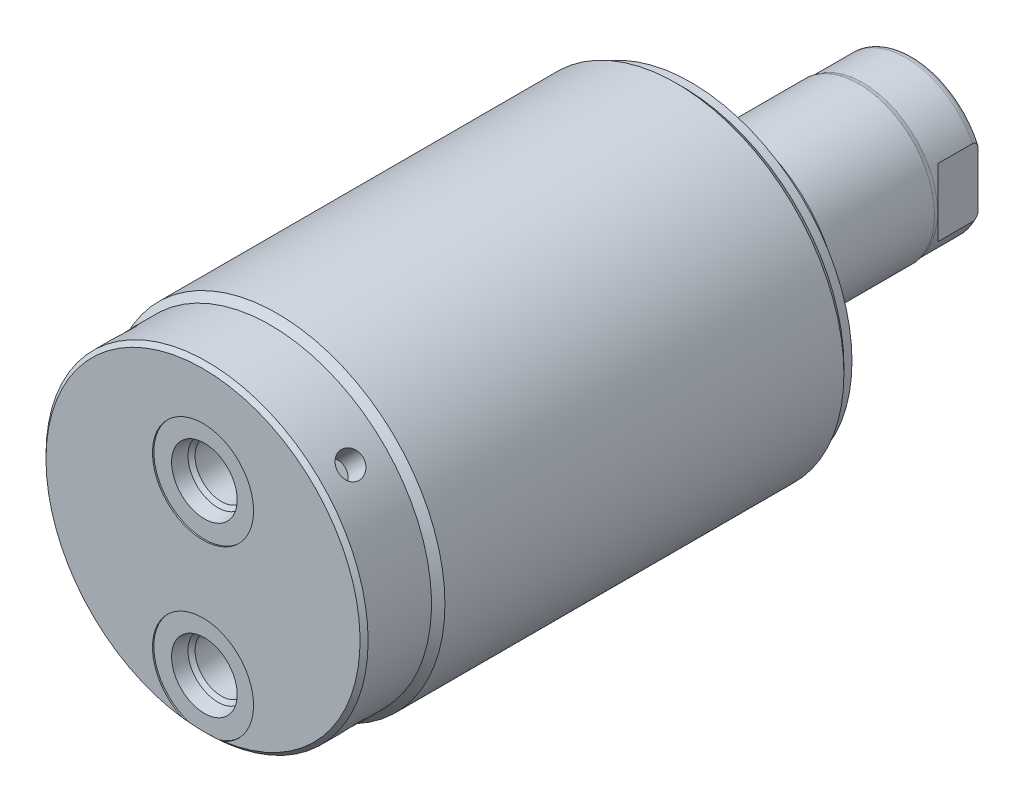
SolidWorks part; units mm, degrees
material "Alloy Steel"
ref_plane "Front Plane" through (0, 0, 0) normal (0, 0, 1) x (1, 0, 0)
ref_plane "Top Plane" through (0, 0, 0) normal (0, 1, 0) x (1, 0, 0)
ref_plane "Right Plane" through (0, 0, 0) normal (1, 0, 0) x (0, 0, -1)
ref_plane "Plane1" through (0, 0, 0) normal (0, 0, 1) x (1, 0, 0)
sketch "Sketch1" plane through (0, 0, 0) normal (0, 0, 1) x (1, 0, 0)
  circle A0 centre (0, 0) radius 31.623
  dimension "D1" = 63.246
extrude "Extrude1" add sketch "Sketch1" along normal blind 91.948
sketch "Sketch2" plane through (0, 0, 0) normal (0, 1, 0) x (1, 0, 0)
  line L0 (31.623, -91.948) -> (31.623, -77.978)
  line L1 (31.623, -77.978) -> (30.353, -79.248)
  line L2 (30.353, -79.248) -> (30.353, -91.948)
  line L3 (30.353, -91.948) -> (31.623, -91.948)
  line L4 (0, 0) -> (0, -24.4965) construction
  line L5 (-31.623, -91.948) -> (31.623, -91.948) construction
  line L6 (31.623, -91.948) -> (31.623, 0) construction
  dimension "D1" = 12.7
  dimension "D2" = 60.706
  dimension "D3" = 45
revolve "Cut-Revolve1" cut sketch "Sketch2" angle 360 about L4
sketch "Sketch3" plane through (0, 0, 0) normal (0, 1, 0) x (1, 0, 0)
  line L0 (30.353, 0) -> (30.353, -1.524)
  line L1 (30.353, -1.524) -> (31.623, -2.794)
  line L2 (31.623, -2.794) -> (31.623, 0)
  line L3 (31.623, 0) -> (30.353, 0)
  line L4 (0, 0) -> (0, 3.0455) construction
  line L6 (31.623, 0) -> (-31.623, 0) construction
  line L7 (31.623, -77.978) -> (31.623, 0) construction
  dimension "D1" = 45
  dimension "D2" = 1.524
  dimension "D3" = 60.706
revolve "Cut-Revolve2" cut sketch "Sketch3" angle 360 about L4
sketch "S2D0002" plane through (0, 0, 0) normal (1, 0, 0) x (0, -1, 0)
  line L0 (-4.9403, -91.694) -> (-1.6002, -91.694)
  line L1 (-4.9403, -91.694) -> (-5.4829, -89.1413)
  line L2 (-5.4829, -89.1413) -> (-6.1468, -88.4774)
  line L3 (-6.1468, -88.4774) -> (-6.1468, -77.724)
  line L4 (-6.1468, -77.724) -> (-11.1252, -77.724)
  line L5 (-11.1252, -77.724) -> (-11.1252, -91.948)
  line L6 (-11.1252, -14.6685) -> (-11.1252, 0.6985) construction
  line L8 (-1.6002, -91.694) -> (-1.6002, -91.948)
  line L9 (-30.353, -91.948) -> (30.353, -91.948) construction
  line L10 (-1.6002, -91.948) -> (-11.1252, -91.948)
  dimension "D1" = 19.05
  dimension "D2" = 9.9568
  dimension "D3" = 0.254
  dimension "D4" = 12.3698
  dimension "D5" = 12
  dimension "D6" = 45
  dimension "D7" = 2.5527
  dimension "D8" = 13.97
  dimension "D9" = 11.1252
revolve "Cut-Revolve3" cut sketch "S2D0002" angle 360 about L6
chamfer "Chamfer1" distance 0.762 angle 45 1 edges at (-30.353, 0, 91.948)
sketch "Sketch6" plane through (0, 0, 0) normal (0, 0, -1) x (-1, 0, 0)
  circle A0 centre (0, 0) radius 22.225
  circle A1 centre (0, 0) radius 31.623 construction
  dimension "D1" = 44.45
extrude "Extrude2" add sketch "Sketch6" along normal blind 5.969
sketch "Sketch7" plane through (0, 0, 0) normal (1, 0, 0) x (0, 0, -1)
  line L0 (5.969, 0) -> (5.969, -14.2875)
  line L1 (5.969, -14.2875) -> (41.529, -14.2875)
  line L2 (41.529, -14.2875) -> (41.529, 0)
  line L3 (41.529, 0) -> (5.969, 0)
  line L4 (0, 0) -> (9.7123, 0) construction
  line L5 (5.969, -22.225) -> (5.969, 22.225) construction
  dimension "D1" = 28.575
  dimension "D2" = 35.56
revolve "Revolve1" add sketch "Sketch7" angle 360 about L4
sketch "S2D0001" plane through (0, 0, 0) normal (0, 1, 0) x (1, 0, 0)
  line L0 (5.5499, 39.4613) -> (5.5499, 25.146)
  line L1 (5.5499, 25.146) -> (0, 25.146)
  line L2 (6.7437, 41.529) -> (0, 41.529)
  line L3 (0, 41.529) -> (0, 25.146)
  line L4 (5.5499, 39.4613) -> (6.7437, 41.529)
  line L5 (0, -31.3084) -> (0, 2.765) construction
  line L6 (14.2875, 41.529) -> (-14.2875, 41.529) construction
  dimension "D1" = 13.4874
  dimension "D2" = 30
  dimension "D3" = 16.383
  dimension "D4" = 11.0998
revolve "Cut-Revolve5" cut sketch "S2D0001" angle 360 about L5
ref_plane "Plane8" through (0, 0, 0) normal (1, 0, 0) x (0, -1, 0)
sketch "Sketch9" plane through (0, 0, 0) normal (1, 0, 0) x (0, -1, 0)
  line L0 (-14.2875, 31.623) -> (-14.097, 32.385)
  line L1 (-14.097, 32.385) -> (-14.097, 40.513)
  line L2 (0, 12.6594) -> (0, 20.8178) construction
  line L3 (14.2875, 41.529) -> (-14.2875, 41.529) construction
  line L4 (-13.7089, 41.529) -> (-14.2875, 41.529)
  line L5 (-14.2875, 41.529) -> (-14.2875, 31.623)
  arc A0 (-13.7089, 41.529) -> (-14.097, 40.513) centre (-12.573, 40.513) ccw
  dimension "D1" = 1.524
  dimension "D2" = 1.016
  dimension "D3" = 28.194
  dimension "D4" = 0.762
  dimension "D5" = 9.144
revolve "Cut-Revolve6" cut sketch "Sketch9" angle 360 about L2
sketch "Sketch13" plane through (0, 0, 0) normal (0, 1, 0) x (1, 0, 0)
  line L0 (12.573, 41.529) -> (12.573, 33.9598)
  line L1 (12.573, 33.9598) -> (14.2875, 32.2453)
  line L2 (-12.573, 41.529) -> (-12.573, 33.9598)
  line L3 (-12.573, 33.9598) -> (-14.2875, 32.2453)
  line L4 (13.7089, 41.529) -> (-13.7089, 41.529) construction
  line L5 (0, 13.7262) -> (0, 20.767) construction
  line L6 (14.2875, 32.2453) -> (14.2875, 41.529)
  line L8 (12.573, 41.529) -> (14.2875, 41.529)
  line L10 (-14.2875, 32.2453) -> (-14.2875, 41.529)
  line L11 (-12.573, 41.529) -> (-14.2875, 41.529)
  line L12 (14.2875, 5.969) -> (14.2875, 31.623) construction
  dimension "D1" = 25.146
  dimension "D2" = 135
  dimension "D3" = 7.5692
extrude "Cut-Extrude4" cut sketch "Sketch13" against normal mid plane 39.685
ref_plane "Plane13" through (0, 0, 0) normal (0.7071, 0.7071, 0) x (0, 0, -1)
hole_wizard "Hole1" positions "3DSketch2" profile "Sketch14" legacy
sketch3d "3DSketch2"
  point P0 (-21.4628, 21.4628, 85.598)
  dimension "D1" = 6.35
sketch "Sketch14" plane through (-21.4628, 21.4628, 85.598) normal (0, 0, 1) x (-0.7071, -0.7071, 0)
  line L0 (0, 0) -> (0, 4.7498)
  line L1 (0, 4.7498) -> (2.3749, 4.7498)
  line L2 (2.3749, 4.7498) -> (2.3749, 0)
  line L3 (2.3749, 0) -> (0, 0)
  line L4 (0, 110) -> (0, -10) construction
  dimension "Diameter" = 4.7498
  dimension "Depth" = 4.7498
pattern_circular "CirPattern1" count 4 over 360 about axis through (0, 0, 0) along (0, 0, 1) of "Hole1"
pattern_linear "LPattern2" count 2 spacing 31.75 along (0, -1, 0) of "Cut-Revolve3"
